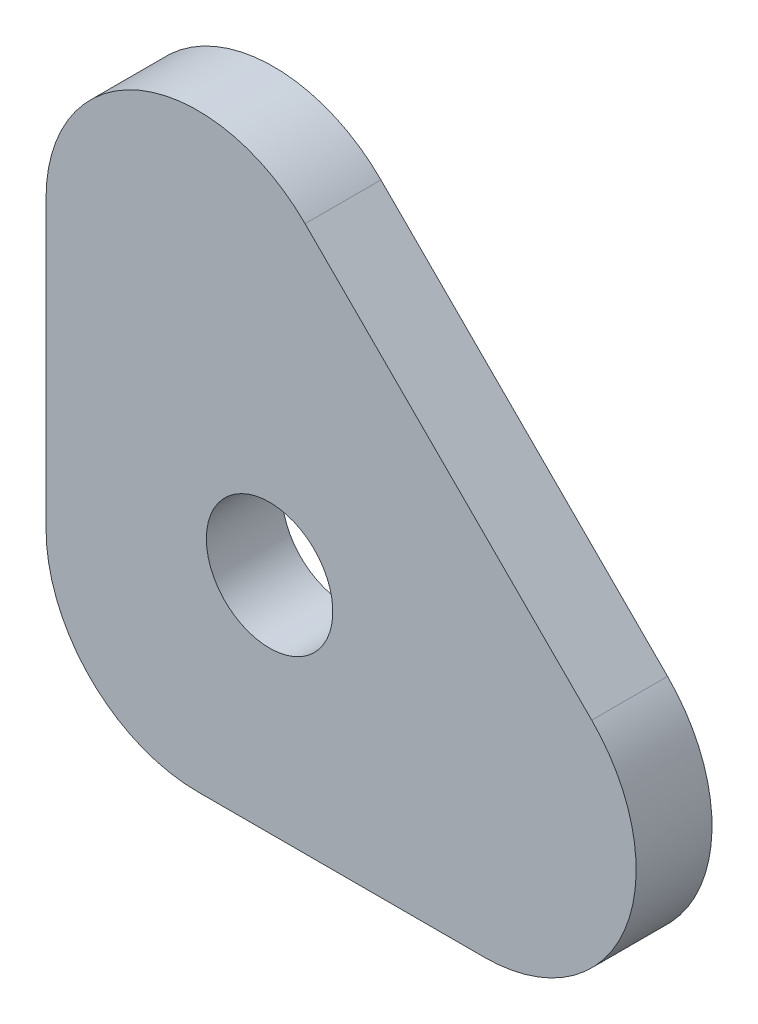
SolidWorks part; units mm, degrees
material "1.0553 (S355J0)"
ref_plane "Front Plane" through (0, 0, 0) normal (0, 0, 1) x (1, 0, 0)
ref_plane "Top Plane" through (0, 0, 0) normal (0, 1, 0) x (1, 0, 0)
ref_plane "Right Plane" through (0, 0, 0) normal (1, 0, 0) x (0, 0, -1)
sketch "Sketch1" plane through (0, 0, 0) normal (0, 0, 1) x (1, 0, 0)
  line L0 (-625, 95.7574) -> (95.7574, -625) construction
  line L1 (-296.4411, -232.8015) -> (-328.2609, -264.6213) construction
  line L2 (-328.2609, -264.6213) -> (-264.6213, -328.2609) construction
  line L3 (-264.6213, -328.2609) -> (-232.8015, -296.4411) construction
  line L4 (-253.2868, -275.9558) -> (-275.9558, -253.2868)
  line L7 (-264.6213, -264.6213) -> (0, 0) construction
  line L8 (-296.4411, -261.7721) -> (-296.4411, -284.4411)
  line L9 (-284.4411, -296.4411) -> (-261.7721, -296.4411)
  line L10 (-264.6213, -264.6213) -> (-296.4411, -296.4411) construction
  circle A0 centre (-278.7635, -278.7635) radius 5
  arc A1 (-261.7721, -296.4411) -> (-253.2868, -275.9558) centre (-261.7721, -284.4411) ccw
  arc A2 (-296.4411, -284.4411) -> (-284.4411, -296.4411) centre (-284.4411, -284.4411) ccw
  arc A3 (-296.4411, -261.7721) -> (-275.9558, -253.2868) centre (-284.4411, -261.7721) cw
  dimension "D4" = 10
  dimension "D5" = 12
  dimension "D1" = 90
  dimension "D2" = 45
  dimension "D3" = 20
extrude "Boss-Extrude1" add sketch "Sketch1" along normal blind 6 from surface
